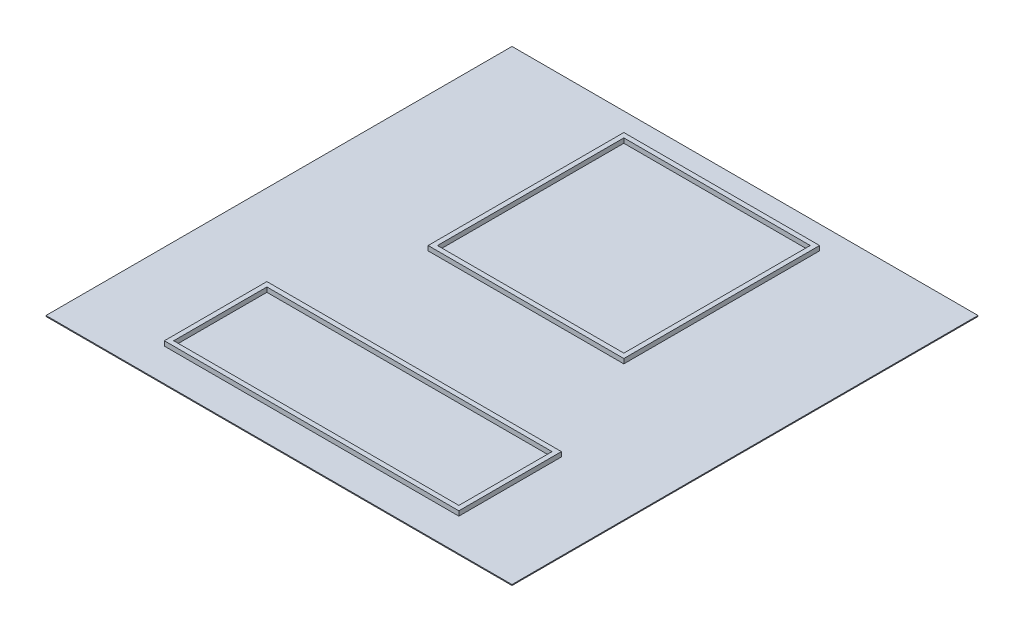
SolidWorks part; units mm, degrees
ref_plane "Front" through (0, 0, 0) normal (0, 0, 1) x (1, 0, 0)
ref_plane "Top" through (0, 0, 0) normal (0, 1, 0) x (1, 0, 0)
ref_plane "Right" through (0, 0, 0) normal (1, 0, 0) x (0, 0, -1)
sketch "Sketch1" plane through (0, 0, 0) normal (0, 1, 0) x (1, 0, 0)
  line L1 (0, 0) -> (5000, 0)
  line L2 (0, 0) -> (0, -5000)
  line L3 (0, -5000) -> (5000, -5000)
  line L4 (5000, 0) -> (5000, -5000)
  dimension "D1" = 5000
  dimension "D2" = 5000
extrude "Boss-Extrude1" add sketch "Sketch1" along normal blind 10
sketch "Sketch2" plane through (0, 10, 0) normal (0, 1, 0) x (1, 0, 0)
  line L0 (0, 0) -> (0, -5000) construction
  line L1 (1500, -300) -> (3500, -300)
  line L2 (1500, -300) -> (1500, -2300)
  line L3 (1500, -2300) -> (3500, -2300)
  line L4 (3500, -300) -> (3500, -2300)
  line L5 (970, -3600) -> (4030, -3600)
  line L6 (970, -3600) -> (970, -4600)
  line L7 (970, -4600) -> (4030, -4600)
  line L8 (4030, -3600) -> (4030, -4600)
  line L9 (5000, 0) -> (0, 0) construction
  line L10 (1450, -250) -> (1450, -2350)
  line L11 (1450, -2350) -> (3550, -2350)
  line L12 (3550, -250) -> (3550, -2350)
  line L13 (1450, -250) -> (3550, -250)
  line L14 (920, -3550) -> (4080, -3550)
  line L15 (4080, -3550) -> (4080, -4650)
  line L16 (920, -4650) -> (4080, -4650)
  line L17 (920, -3550) -> (920, -4650)
  dimension "D1" = 2000
  dimension "D2" = 2000
  dimension "D3" = 1500
  dimension "D4" = 300
  dimension "D5" = 1000
  dimension "D6" = 3060
  dimension "D7" = 970
  dimension "D8" = 1300
  dimension "D9" = 50
extrude "Boss-Extrude2" add sketch "Sketch2" along normal blind 50
